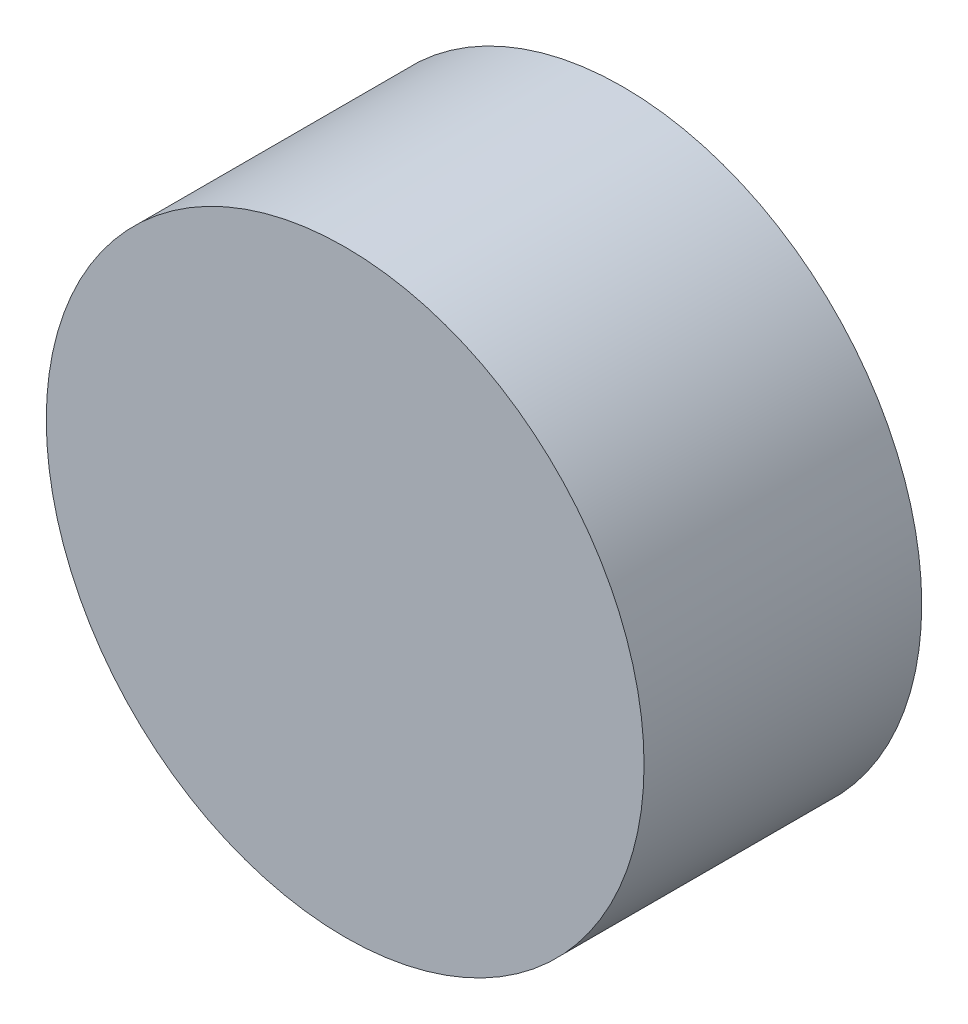
SolidWorks part; units mm, degrees
material "6061-T6 (SS)"
ref_plane "Front Plane" through (0, 0, 0) normal (0, 0, 1) x (1, 0, 0)
ref_plane "Top Plane" through (0, 0, 0) normal (0, 1, 0) x (1, 0, 0)
ref_plane "Right Plane" through (0, 0, 0) normal (1, 0, 0) x (0, 0, -1)
sketch "Sketch1" plane through (0, 0, 0) normal (0, 0, 1) x (1, 0, 0)
  circle A0 centre (0, 0) radius 30.7594
  dimension "D1" = 61.5188
extrude "Boss-Extrude1" add sketch "Sketch1" along normal blind 28.575
